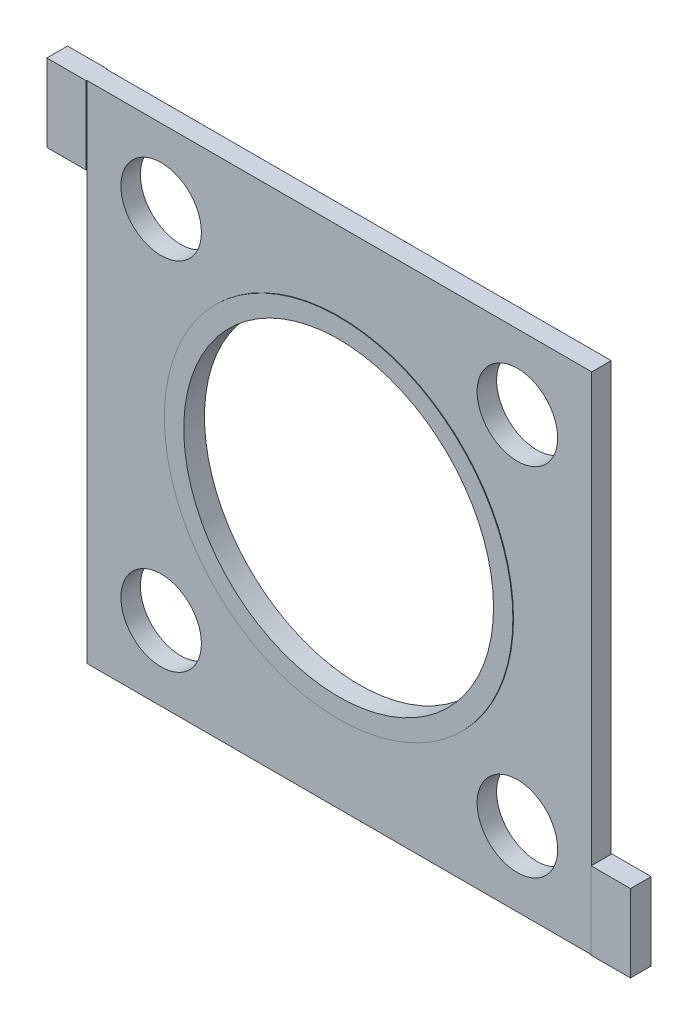
SolidWorks part; units mm, degrees
ref_plane "Front Plane" through (0, 0, 0) normal (0, 0, 1) x (1, 0, 0)
ref_plane "Top Plane" through (0, 0, 0) normal (0, 1, 0) x (1, 0, 0)
ref_plane "Right Plane" through (0, 0, 0) normal (1, 0, 0) x (0, 0, -1)
sketch "Sketch1" plane through (0, 0, 0) normal (0, 0, 1) x (1, 0, 0)
  line L1 (-20.701, 20.701) -> (20.701, 20.701)
  line L2 (-20.701, 20.701) -> (-20.701, -20.701)
  line L3 (-20.701, -20.701) -> (20.701, -20.701)
  line L4 (20.701, 20.701) -> (20.701, -20.701)
  dimension "D1" = 41.402
  dimension "D2" = 41.402
  dimension "D3" = 20.701
  dimension "D4" = 20.701
extrude "Boss-Extrude1" add sketch "Sketch1" along normal blind 0.7988 and the other way blind 0.7988
sketch "Sketch2" plane through (0, 0, 0) normal (0, 0, 1) x (1, 0, 0)
  line L1 (-20.701, 20.701) -> (-23.9293, 20.701)
  line L2 (-20.701, 20.701) -> (-20.701, 14.351)
  line L3 (-20.701, 14.351) -> (-23.9293, 14.351)
  line L4 (-23.9293, 20.701) -> (-23.9293, 14.351)
  line L5 (20.701, -20.701) -> (23.9293, -20.701)
  line L6 (20.701, -20.701) -> (20.701, -14.351)
  line L7 (20.701, -14.351) -> (23.9293, -14.351)
  line L8 (23.9293, -20.701) -> (23.9293, -14.351)
  dimension "D1" = 6.35
  dimension "D2" = 3.2283
  dimension "D3" = 3.2283
  dimension "D4" = 6.35
extrude "Boss-Extrude2" add sketch "Sketch2" along normal blind 0.7988 and the other way blind 0.7988
sketch "Sketch3" plane through (0, 0, 0.7988) normal (0, 0, 1) x (1, 0, 0)
  circle A0 centre (0, 0) radius 12.7
  dimension "D1" = 25.4
extrude "Cut-Extrude1" cut sketch "Sketch3" against normal through all
sketch "Sketch4" plane through (0, 0, 0.7988) normal (0, 0, 1) x (1, 0, 0)
  circle A0 centre (0, 0) radius 14.2875
  circle A1 centre (0, 0) radius 12.7
  dimension "D1" = 28.575
extrude "Boss-Extrude3" add sketch "Sketch4" along normal blind 0.0508
sketch "Sketch5" plane through (0, 0, 0.7988) normal (0, 0, 1) x (1, 0, 0)
  line L1 (-23.9293, 20.701) -> (-20.701, 20.701)
  line L2 (-23.9293, 20.701) -> (-23.9293, 14.351)
  line L3 (-23.9293, 14.351) -> (-20.701, 14.351)
  line L4 (-20.701, 20.701) -> (-20.701, 14.351)
  line L5 (23.9293, -20.701) -> (20.701, -20.701)
  line L6 (23.9293, -20.701) -> (23.9293, -14.351)
  line L7 (23.9293, -14.351) -> (20.701, -14.351)
  line L8 (20.701, -20.701) -> (20.701, -14.351)
extrude "Boss-Extrude4" add sketch "Sketch5" along normal blind 0.0508
mirror "Mirror3" about plane through (0, 0, 0) normal (0, 0, 1) of "Boss-Extrude4", "Boss-Extrude3"
sketch "Sketch6" plane through (0, 0, 0.7988) normal (0, 0, 1) x (1, 0, 0)
  circle A0 centre (-14.605, 14.605) radius 3.302
  circle A1 centre (14.605, 14.605) radius 3.302
  point P7 (0, 0)
  dimension "D1" = 6.604
  dimension "D2" = 6.604
  dimension "D3" = 29.21
  dimension "D4" = 14.605
  dimension "D5" = 14.605
  dimension "D6" = 14.605
extrude "Cut-Extrude2" cut sketch "Sketch6" against normal through all
mirror "Mirror4" about plane through (0, 0, 0) normal (0, 1, 0) of "Cut-Extrude2"
equation "\"D2@Sketch1\"=\"D1@Sketch1\""
equation "\"D3@Sketch1\"=\"D1@Sketch1\"/2"
equation "\"D4@Sketch1\"=\"D2@Sketch1\"/2"
equation "\"D2@Sketch6\"=\"D1@Sketch6\""
equation "\"D4@Sketch6\"=\"D3@Sketch6\"/2"
equation "\"D5@Sketch6\"=\"D4@Sketch6\""
equation "\"D6@Sketch6\"=\"D4@Sketch6\""
